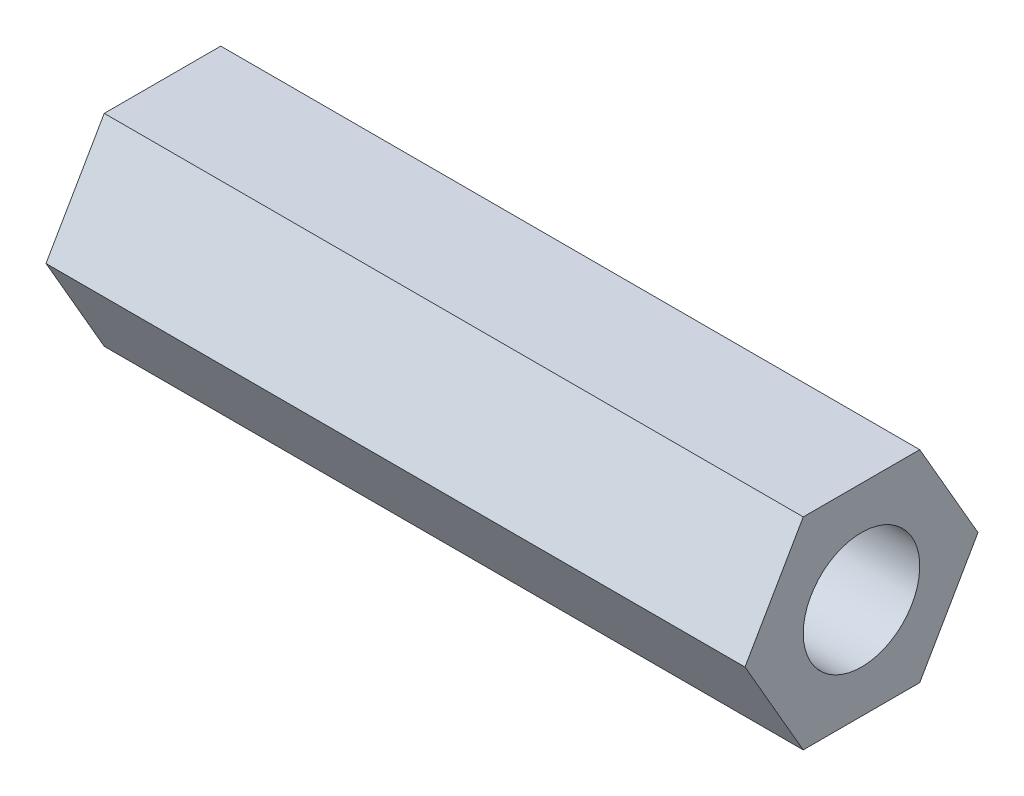
SolidWorks part; units mm, degrees
material "5052-H32"
ref_plane "Front Plane" through (0, 0, 0) normal (0, 0, 1) x (1, 0, 0)
ref_plane "Top Plane" through (0, 0, 0) normal (0, 1, 0) x (1, 0, 0)
ref_plane "Right Plane" through (0, 0, 0) normal (1, 0, 0) x (0, 0, -1)
sketch "Sketch1" plane through (0, 0, 0) normal (1, 0, 0) x (0, 0, -1)
  line L1 (6.35, 0) -> (3.175, 5.4993)
  line L2 (3.175, 5.4993) -> (-3.175, 5.4993)
  line L3 (-3.175, 5.4993) -> (-6.35, 0)
  line L4 (-6.35, 0) -> (-3.175, -5.4993)
  line L5 (-3.175, -5.4993) -> (3.175, -5.4993)
  line L6 (3.175, -5.4993) -> (6.35, 0)
  circle A0 centre (0, 0) radius 5.4993 construction
  dimension "D1" = 6.35
extrude "Boss-Extrude1" add sketch "Sketch1" along normal blind 38.1
sketch "Sketch2" plane through (0, 0, 0) normal (-1, 0, 0) x (0, 0, 1)
  circle A0 centre (0, 0) radius 3.175
  dimension "D1" = 6.35
extrude "Cut-Extrude1" cut sketch "Sketch2" against normal through all
